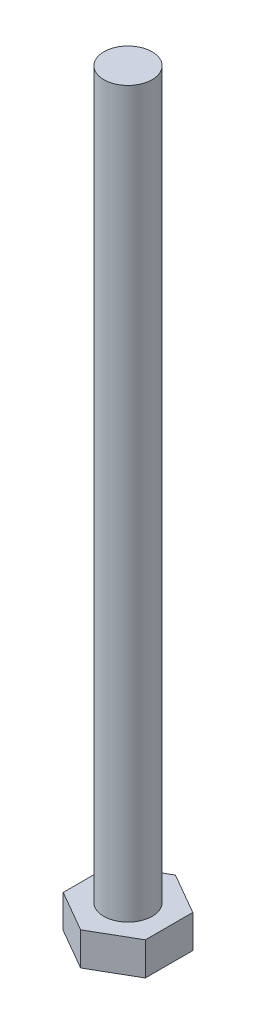
SolidWorks part; units mm, degrees
ref_plane "Спереди" through (0, 0, 0) normal (0, 0, 1) x (1, 0, 0)
ref_plane "Сверху" through (0, 0, 0) normal (0, 1, 0) x (1, 0, 0)
ref_plane "Справа" through (0, 0, 0) normal (1, 0, 0) x (0, 0, -1)
sketch "Эскиз1" plane through (0, 0, 0) normal (0, 1, 0) x (1, 0, 0)
  line L1 (8.5, -4.9075) -> (8.5, 4.9075)
  line L2 (8.5, 4.9075) -> (0, 9.815)
  line L3 (0, 9.815) -> (-8.5, 4.9075)
  line L4 (-8.5, 4.9075) -> (-8.5, -4.9075)
  line L5 (-8.5, -4.9075) -> (0, -9.815)
  line L6 (0, -9.815) -> (8.5, -4.9075)
  circle A0 centre (0, 0) radius 8.5 construction
extrude "Бобышка-Вытянуть1" add sketch "Эскиз1" along normal blind 8
sketch "Эскиз2" plane through (0, 8, 0) normal (0, 1, 0) x (1, 0, 0)
  circle A0 centre (0, 0) radius 5
extrude "Бобышка-Вытянуть2" add sketch "Эскиз2" along normal blind 150
chamfer "Фаска1" distance 2 angle 30 6 edges at (4.25, 0, -7.3612) (8.5, 0, 0) (4.25, 0, 7.3612) (-4.25, 0, 7.3612) (-8.5, 0, 0) (-4.25, 0, -7.3612)
